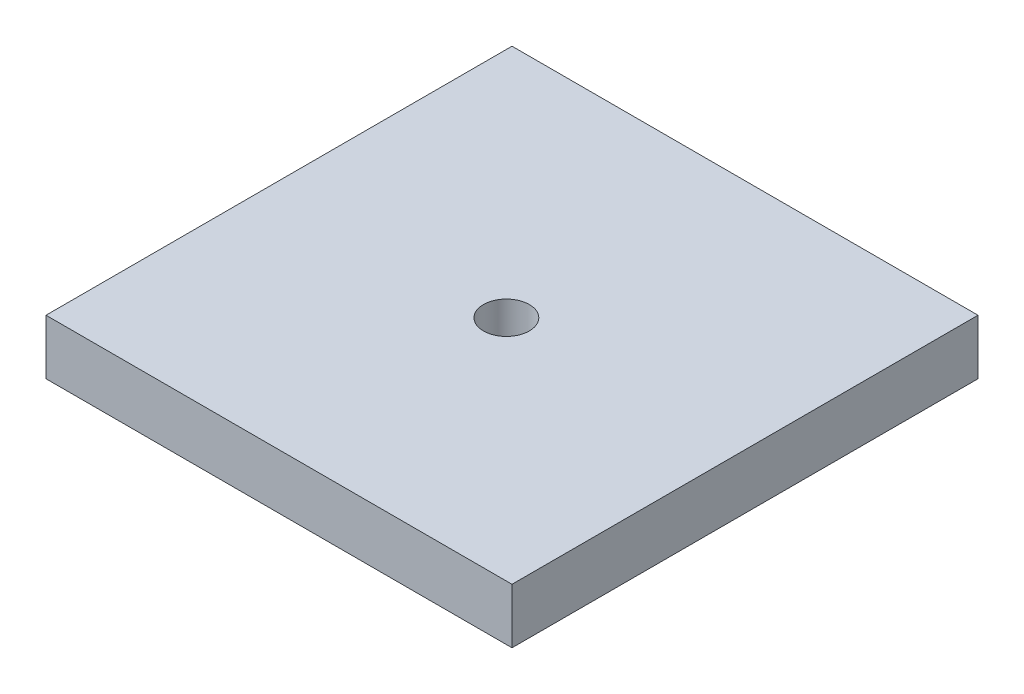
SolidWorks part; units mm, degrees
ref_plane "Front Plane" through (0, 0, 0) normal (0, 0, 1) x (1, 0, 0)
ref_plane "Top Plane" through (0, 0, 0) normal (0, 1, 0) x (1, 0, 0)
ref_plane "Right Plane" through (0, 0, 0) normal (1, 0, 0) x (0, 0, -1)
sketch "Sketch1" plane through (0, 0, 0) normal (0, 1, 0) x (1, 0, 0)
  line L1 (-12.7, 12.7) -> (12.7, 12.7)
  line L2 (-12.7, 12.7) -> (-12.7, -12.7)
  line L3 (-12.7, -12.7) -> (12.7, -12.7)
  line L4 (12.7, 12.7) -> (12.7, -12.7)
  line L5 (-12.7, 12.7) -> (12.7, -12.7) construction
  line L6 (-12.7, -12.7) -> (12.7, 12.7) construction
  point P0 (0, 0)
  dimension "D1" = 25.4
  dimension "D2" = 25.4
extrude "Boss-Extrude1" add sketch "Sketch1" along normal blind 3
hole_wizard "M3x0.5 Tapped Hole1" positions "3DSketch1" profile "Sketch2" tap size "M3x0.5" standard "ANSI Metric"
sketch3d "3DSketch1"
  point P0 (0, 0, 0)
  point P3 (0, 0, 0)
  point P5 (-0.034, 3, 0.272)
sketch "Sketch2" plane through (-0.034, 3, 0.272) normal (1, 0, 0) x (0, 0, 1)
  line L0 (0, 0) -> (0, 3)
  line L1 (0, 3) -> (1.25, 3)
  line L2 (1.25, 3) -> (1.25, 0)
  line L5 (1.25, 0) -> (0, 0)
  line L11 (0, -6.35) -> (0, 107.95) construction
  dimension "Thru Tap Drill Dia." = 2.5
  dimension "Thru Tap Drill Depth" = 3
cosmetic thread "Hole Thread1" parameters "D2"=3
cosmetic thread "Hole Thread2" parameters "D2"=3
cosmetic thread "Hole Thread3" parameters "D2"=3
